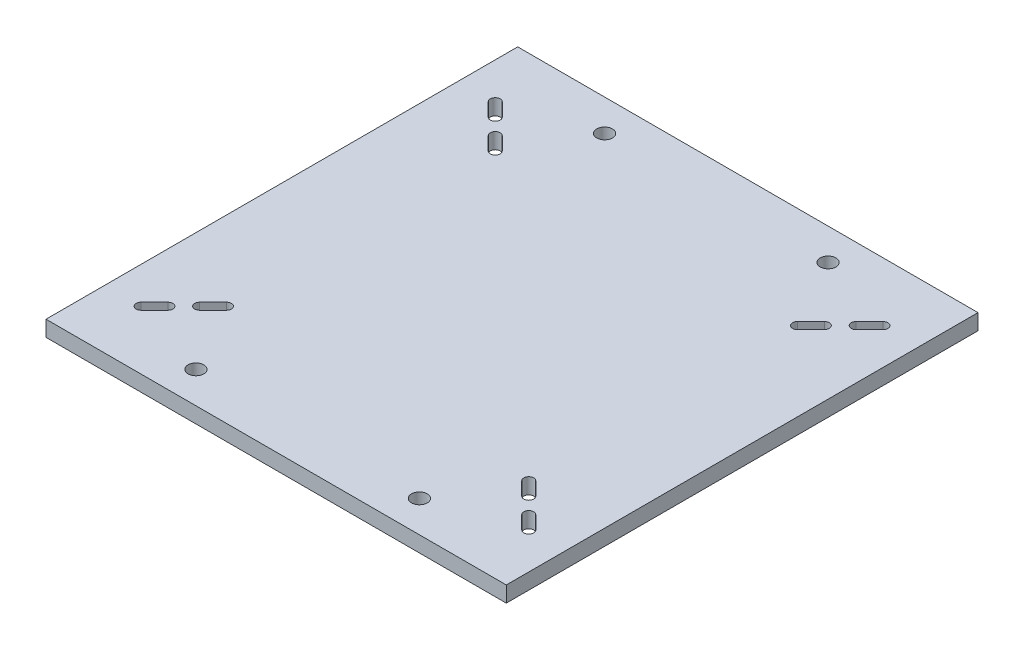
SolidWorks part; units mm, degrees
material "6061-T6 (SS)"
ref_plane "Front Plane" through (0, 0, 0) normal (0, 0, 1) x (1, 0, 0)
ref_plane "Top Plane" through (0, 0, 0) normal (0, 1, 0) x (1, 0, 0)
ref_plane "Right Plane" through (0, 0, 0) normal (1, 0, 0) x (0, 0, -1)
sketch "Sketch1" plane through (0, 0, 0) normal (0, 1, 0) x (1, 0, 0)
  line L1 (0, 0) -> (185.4, 0)
  line L2 (0, 0) -> (0, -190)
  line L3 (0, -190) -> (185.4, -190)
  line L4 (185.4, 0) -> (185.4, -190)
  dimension "D1" = 185.4
  dimension "D2" = 190
extrude "base plate" add sketch "Sketch1" against normal blind 6.35
sketch "center lines" plane through (0, 0, 0) normal (0, 1, 0) x (1, 0, 0)
  line L0 (92.7, 0) -> (92.7, -190) construction
  line L1 (185.4, 0) -> (0, 0) construction
  line L2 (0, -190) -> (185.4, -190) construction
  line L3 (0, -95) -> (185.4, -95) construction
  line L4 (0, 0) -> (0, -190) construction
  line L5 (185.4, -190) -> (185.4, 0) construction
sketch "Sketch3" plane through (0, 0, 0) normal (0, 1, 0) x (1, 0, 0)
  line L0 (1.825, -168.3487) -> (12.6013, -179.125)
  line L1 (12.6013, -179.125) -> (46.7263, -145)
  line L2 (46.7263, -145) -> (35.95, -134.2237)
  line L3 (35.95, -134.2237) -> (1.825, -168.3487)
  line L4 (14.6222, -166.3278) -> (20.0104, -160.9396) construction
  line L5 (13.208, -164.9135) -> (18.5962, -159.5254)
  line L6 (16.0365, -167.742) -> (21.4246, -162.3538)
  line L7 (0, -190) -> (185.4, -190) construction
  line L8 (31.8191, -149.1309) -> (26.4309, -154.5191) construction
  line L9 (33.2333, -150.5451) -> (27.8451, -155.9333)
  line L10 (92.7, 0) -> (92.7, -190) construction
  line L11 (0, -95) -> (185.4, -95) construction
  line L12 (46.7263, -45) -> (35.95, -55.7763)
  line L13 (12.6013, -10.875) -> (46.7263, -45)
  line L14 (1.825, -21.6513) -> (12.6013, -10.875)
  line L15 (35.95, -55.7763) -> (1.825, -21.6513)
  line L16 (172.7987, -10.875) -> (138.6737, -45)
  line L17 (183.575, -21.6513) -> (172.7987, -10.875)
  line L18 (149.45, -55.7763) -> (183.575, -21.6513)
  line L19 (138.6737, -45) -> (149.45, -55.7763)
  line L20 (138.6737, -145) -> (149.45, -134.2237)
  line L21 (172.7987, -179.125) -> (138.6737, -145)
  line L22 (183.575, -168.3487) -> (172.7987, -179.125)
  line L23 (149.45, -134.2237) -> (183.575, -168.3487)
  line L24 (30.4049, -147.7167) -> (25.0167, -153.1049)
  line L25 (14.6222, -23.6722) -> (20.0104, -29.0604) construction
  line L26 (13.208, -25.0865) -> (18.5962, -30.4746)
  line L27 (16.0365, -22.258) -> (21.4246, -27.6462)
  line L28 (31.8191, -40.8691) -> (26.4309, -35.4809) construction
  line L29 (33.2333, -39.4549) -> (27.8451, -34.0667)
  line L30 (30.4049, -42.2833) -> (25.0167, -36.8951)
  line L31 (170.7778, -23.6722) -> (165.3896, -29.0604) construction
  line L32 (172.192, -25.0865) -> (166.8038, -30.4746)
  line L33 (169.3635, -22.258) -> (163.9754, -27.6462)
  line L34 (153.5809, -40.8691) -> (158.9691, -35.4809) construction
  line L35 (152.1667, -39.4549) -> (157.5549, -34.0667)
  line L36 (154.9951, -42.2833) -> (160.3833, -36.8951)
  line L37 (153.5809, -149.1309) -> (158.9691, -154.5191) construction
  line L38 (152.1667, -150.5451) -> (157.5549, -155.9333)
  line L39 (154.9951, -147.7167) -> (160.3833, -153.1049)
  line L40 (170.7778, -166.3278) -> (165.3896, -160.9396) construction
  line L41 (172.192, -164.9135) -> (166.8038, -159.5254)
  line L42 (169.3635, -167.742) -> (163.9754, -162.3538)
  line L43 (35.95, -145) -> (35.95, -134.2237)
  line L44 (46.7263, -145) -> (35.95, -145)
  line L45 (35.95, -45) -> (35.95, -55.7763)
  line L46 (46.7263, -45) -> (35.95, -45)
  line L47 (149.45, -45) -> (149.45, -55.7763)
  line L48 (138.6737, -45) -> (149.45, -45)
  line L49 (149.45, -145) -> (149.45, -134.2237)
  line L50 (138.6737, -145) -> (149.45, -145)
  line L53 (185.4, 0) -> (0, 0) construction
  arc A0 (13.208, -164.9135) -> (16.0365, -167.742) centre (14.6222, -166.3278) ccw
  arc A1 (21.4246, -162.3538) -> (18.5962, -159.5254) centre (20.0104, -160.9396) ccw
  arc A2 (33.2333, -150.5451) -> (30.4049, -147.7167) centre (31.8191, -149.1309) ccw
  arc A3 (25.0167, -153.1049) -> (27.8451, -155.9333) centre (26.4309, -154.5191) ccw
  arc A4 (13.208, -25.0865) -> (16.0365, -22.258) centre (14.6222, -23.6722) cw
  arc A5 (21.4246, -27.6462) -> (18.5962, -30.4746) centre (20.0104, -29.0604) cw
  arc A6 (33.2333, -39.4549) -> (30.4049, -42.2833) centre (31.8191, -40.8691) cw
  arc A7 (25.0167, -36.8951) -> (27.8451, -34.0667) centre (26.4309, -35.4809) cw
  arc A8 (172.192, -25.0865) -> (169.3635, -22.258) centre (170.7778, -23.6722) ccw
  arc A9 (163.9754, -27.6462) -> (166.8038, -30.4746) centre (165.3896, -29.0604) ccw
  arc A10 (152.1667, -39.4549) -> (154.9951, -42.2833) centre (153.5809, -40.8691) ccw
  arc A11 (160.3833, -36.8951) -> (157.5549, -34.0667) centre (158.9691, -35.4809) ccw
  arc A12 (152.1667, -150.5451) -> (154.9951, -147.7167) centre (153.5809, -149.1309) cw
  arc A13 (160.3833, -153.1049) -> (157.5549, -155.9333) centre (158.9691, -154.5191) cw
  arc A14 (172.192, -164.9135) -> (169.3635, -167.742) centre (170.7778, -166.3278) cw
  arc A15 (163.9754, -162.3538) -> (166.8038, -159.5254) centre (165.3896, -160.9396) cw
  point P29 (17.3163, -163.6337)
  point P36 (29.125, -151.825)
  point P44 (17.3163, -26.3663)
  point P51 (29.125, -38.175)
  point P58 (168.0837, -26.3663)
  point P65 (156.275, -38.175)
  point P72 (156.275, -151.825)
  point P79 (168.0837, -163.6337)
  point P84 (21.4246, -159.5254)
  point P85 (25.0167, -155.9333)
  dimension "D6" = 2
  dimension "D10" = 5.08
  dimension "D9" = 5.842
  dimension "D1" = 48.26
  dimension "D2" = 15.24
  dimension "D3" = 45
  dimension "D4" = 100
  dimension "D5" = 113.5
  dimension "D7" = 7.62
  dimension "D8" = 7.62
extrude "slots" cut sketch "Sketch3" against normal through all contours A5 L27 A4 L26 | L33 A9 L32 A8 | L36 A11 L35 A10 | A13 L39 A12 L38 | A15 L42 A14 L41 | L6 A1 L5 A0 | L24 A3 L9 A2 | L30 A7 L29 A6
hole_wizard "Feet connection hole" positions "Sketch6" profile "Sketch7" hole size "1/4" standard "ANSI Inch" end condition through all
sketch "Sketch6" plane through (0, 0, 0) normal (0, 1, 0) x (1, 0, 0)
  line L0 (0, -190) -> (185.4, -190) construction
  line L3 (185.4, 0) -> (0, 0) construction
  line L4 (92.7, 0) -> (92.7, -190) construction
  point P3 (47.7, -177.3)
  point P19 (137.7, -12.7)
  point P33 (47.7, -12.7)
  point P37 (137.7, -177.3)
  dimension "D1" = 12.7
  dimension "D2" = 90
  dimension "D3" = 45
  dimension "D4" = 12.7
sketch "Sketch7" plane through (47.7, 0, 177.3) normal (1, 0, 0) x (0, 0, 1)
  line L0 (0, 0) -> (0, 6.35)
  line L1 (0, 6.35) -> (3.175, 6.35)
  line L2 (3.175, 6.35) -> (3.175, 0)
  line L5 (3.175, 0) -> (0, 0)
  line L11 (0, -6.35) -> (0, 107.95) construction
  dimension "Thru Hole Dia." = 6.35
  dimension "Thru Hole Depth" = 6.35
ref_plane "Center Plane" through (0, 0, 95) normal (0, 0, 1) x (1, 0, 0)
